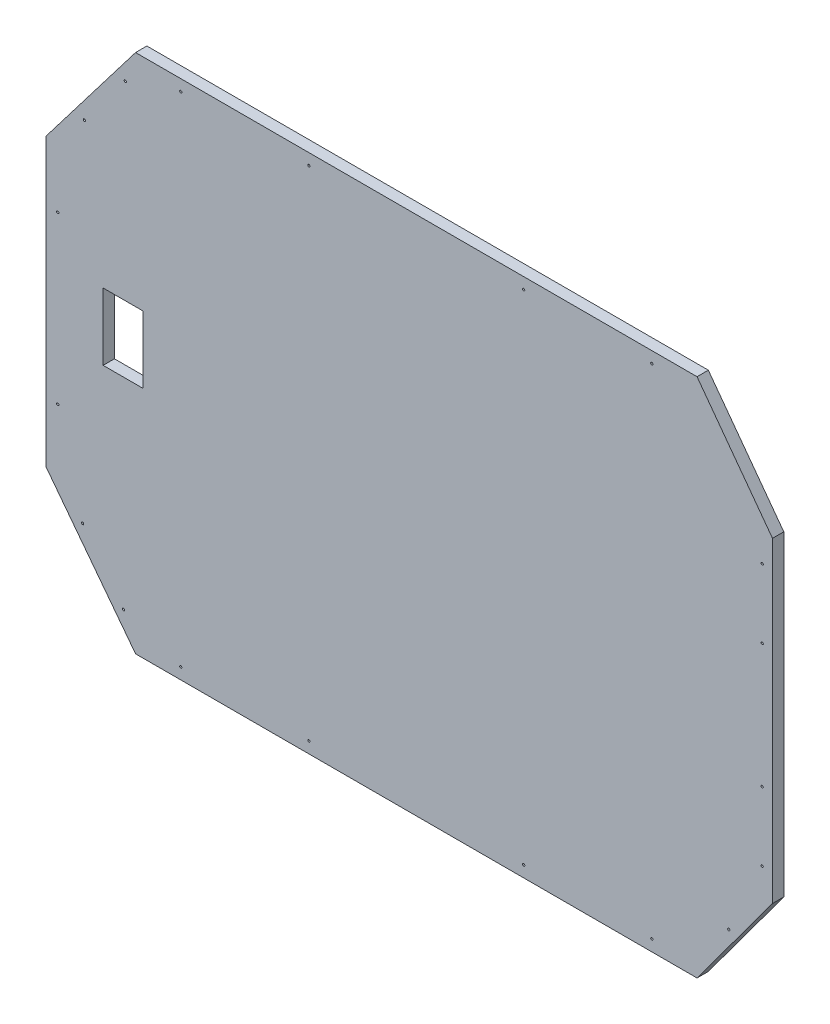
SolidWorks part; units mm, degrees
ref_plane "Front Plane" through (0, 0, 0) normal (0, 0, 1) x (1, 0, 0)
ref_plane "Top Plane" through (0, 0, 0) normal (0, 1, 0) x (1, 0, 0)
ref_plane "Right Plane" through (0, 0, 0) normal (1, 0, 0) x (0, 0, -1)
sketch "Sketch1" plane through (0, 0, 0) normal (0, 0, 1) x (1, 0, 0)
  line L0 (118.58, 345.4877) -> (863.58, 345.4877) construction
  line L1 (0, 500.6804) -> (118.58, 345.4877) construction
  line L2 (0, 881.2704) -> (0, 500.6804) construction
  line L3 (118.58, 1036.4632) -> (0, 881.2704) construction
  line L4 (863.58, 1036.4632) -> (118.58, 1036.4632) construction
  line L5 (963.71, 900.8043) -> (863.58, 1036.4632) construction
  line L6 (963.71, 481.1465) -> (963.71, 900.8043) construction
  line L7 (863.58, 345.4877) -> (963.71, 481.1465) construction
  line L8 (118.58, 345.4877) -> (863.58, 345.4877)
  line L9 (0, 500.6804) -> (118.58, 345.4877)
  line L10 (0, 881.2704) -> (0, 500.6804)
  line L11 (118.58, 1036.4632) -> (0, 881.2704)
  line L12 (863.58, 1036.4632) -> (118.58, 1036.4632)
  line L13 (963.71, 900.8043) -> (863.58, 1036.4632)
  line L14 (963.71, 481.1465) -> (963.71, 900.8043)
  line L15 (863.58, 345.4877) -> (963.71, 481.1465)
  line L60 (52.1694, 933.0769) -> (44.2234, 939.1483)
  line L61 (44.2234, 939.1483) -> (2.5279, 884.5789)
  line L62 (2.5279, 884.5789) -> (2.5279, 710.9754)
  line L63 (2.5279, 710.9754) -> (32.5279, 710.9754)
  line L64 (32.5279, 710.9754) -> (32.5279, 680.9754)
  line L65 (32.5279, 680.9754) -> (2.5279, 680.9754)
  line L66 (2.5279, 680.9754) -> (2.5279, 507.372)
  line L67 (2.5279, 507.372) -> (44.2234, 452.8026)
  line L68 (44.2234, 452.8026) -> (52.1694, 458.874)
  line L69 (52.1694, 458.874) -> (52.236, 458.7868)
  line L70 (52.236, 458.7868) -> (91.9659, 489.1436)
  line L71 (91.9659, 489.1436) -> (128.8173, 440.9139)
  line L72 (128.8173, 440.9139) -> (81.1415, 404.4857)
  line L73 (81.1415, 404.4857) -> (118.58, 355.4877)
  line L74 (118.58, 355.4877) -> (247.5279, 355.4877)
  line L75 (247.5279, 355.4877) -> (247.5279, 421.1462)
  line L76 (247.5279, 421.1462) -> (301.5406, 421.1462)
  line L77 (301.5406, 421.1462) -> (301.5406, 355.4877)
  line L78 (301.5406, 355.4877) -> (439.5279, 355.4877)
  line L79 (439.5279, 355.4877) -> (439.5279, 385.4877)
  line L80 (439.5279, 385.4877) -> (469.5279, 385.4877)
  line L81 (469.5279, 385.4877) -> (469.5279, 355.4877)
  line L82 (469.5279, 355.4877) -> (501.5406, 355.4877)
  line L83 (501.5406, 355.4877) -> (501.5406, 421.1462)
  line L84 (501.5406, 421.1462) -> (555.5406, 421.1462)
  line L85 (555.5406, 421.1462) -> (555.5406, 355.4877)
  line L86 (555.5406, 355.4877) -> (858.5839, 355.4877)
  line L87 (858.5839, 355.4877) -> (894.7004, 404.4193)
  line L88 (894.7004, 404.4193) -> (852.6416, 435.4629)
  line L89 (852.6416, 435.4629) -> (885.5391, 480.0333)
  line L90 (885.5391, 480.0333) -> (927.5979, 448.9897)
  line L91 (927.5979, 448.9897) -> (956.2379, 487.792)
  line L92 (956.2379, 487.792) -> (956.2379, 680.9754)
  line L93 (956.2379, 680.9754) -> (926.2379, 680.9754)
  line L94 (926.2379, 680.9754) -> (926.2379, 710.9754)
  line L95 (926.2379, 710.9754) -> (956.2379, 710.9754)
  line L96 (956.2379, 710.9754) -> (956.2379, 904.1589)
  line L97 (956.2379, 904.1589) -> (927.5979, 942.9612)
  line L98 (927.5979, 942.9612) -> (885.5391, 911.9176)
  line L99 (885.5391, 911.9176) -> (852.6416, 956.4879)
  line L100 (852.6416, 956.4879) -> (894.7004, 987.5316)
  line L101 (894.7004, 987.5316) -> (858.5839, 1036.4632)
  line L102 (858.5839, 1036.4632) -> (555.5406, 1036.4632)
  line L103 (555.5406, 1036.4632) -> (555.5406, 970.8046)
  line L104 (555.5406, 970.8046) -> (501.5406, 970.8046)
  line L105 (501.5406, 970.8046) -> (501.5406, 1036.4632)
  line L106 (501.5406, 1036.4632) -> (469.5279, 1036.4632)
  line L107 (469.5279, 1036.4632) -> (469.5279, 1006.4632)
  line L108 (469.5279, 1006.4632) -> (439.5279, 1006.4632)
  line L109 (439.5279, 1006.4632) -> (439.5279, 1036.4632)
  line L110 (439.5279, 1036.4632) -> (301.5406, 1036.4632)
  line L111 (301.5406, 1036.4632) -> (301.5406, 970.8046)
  line L112 (301.5406, 970.8046) -> (247.5279, 970.8046)
  line L113 (247.5279, 970.8046) -> (247.5279, 1036.4632)
  line L114 (247.5279, 1036.4632) -> (118.58, 1036.4632)
  line L115 (118.58, 1036.4632) -> (81.1415, 987.4652)
  line L116 (81.1415, 987.4652) -> (128.8173, 951.0369)
  line L117 (128.8173, 951.0369) -> (91.9659, 902.8072)
  line L118 (91.9659, 902.8072) -> (52.236, 933.1641)
  line L119 (52.236, 933.1641) -> (52.1694, 933.0769)
  line L120 (52.1694, 933.0769) -> (44.2234, 939.1483)
  line L121 (44.2234, 939.1483) -> (2.5279, 884.5789)
  line L122 (2.5279, 884.5789) -> (2.5279, 710.9754)
  line L123 (2.5279, 710.9754) -> (32.5279, 710.9754)
  line L124 (32.5279, 710.9754) -> (32.5279, 680.9754)
  line L125 (32.5279, 680.9754) -> (2.5279, 680.9754)
  line L126 (2.5279, 680.9754) -> (2.5279, 507.372)
  line L127 (2.5279, 507.372) -> (44.2234, 452.8026)
  line L128 (44.2234, 452.8026) -> (52.1694, 458.874)
  line L129 (52.1694, 458.874) -> (52.236, 458.7868)
  line L130 (52.236, 458.7868) -> (91.9659, 489.1436)
  line L131 (91.9659, 489.1436) -> (128.8173, 440.9139)
  line L132 (128.8173, 440.9139) -> (81.1415, 404.4857)
  line L133 (81.1415, 404.4857) -> (118.58, 355.4877)
  line L134 (118.58, 355.4877) -> (247.5279, 355.4877)
  line L135 (247.5279, 355.4877) -> (247.5279, 421.1462)
  line L136 (247.5279, 421.1462) -> (301.5406, 421.1462)
  line L137 (301.5406, 421.1462) -> (301.5406, 355.4877)
  line L138 (301.5406, 355.4877) -> (439.5279, 355.4877)
  line L139 (439.5279, 355.4877) -> (439.5279, 385.4877)
  line L140 (439.5279, 385.4877) -> (469.5279, 385.4877)
  line L141 (469.5279, 385.4877) -> (469.5279, 355.4877)
  line L142 (469.5279, 355.4877) -> (501.5406, 355.4877)
  line L143 (501.5406, 355.4877) -> (501.5406, 421.1462)
  line L144 (501.5406, 421.1462) -> (555.5406, 421.1462)
  line L145 (555.5406, 421.1462) -> (555.5406, 355.4877)
  line L146 (555.5406, 355.4877) -> (858.5839, 355.4877)
  line L147 (858.5839, 355.4877) -> (894.7004, 404.4193)
  line L148 (894.7004, 404.4193) -> (852.6416, 435.4629)
  line L149 (852.6416, 435.4629) -> (885.5391, 480.0333)
  line L150 (885.5391, 480.0333) -> (927.5979, 448.9897)
  line L151 (927.5979, 448.9897) -> (956.2379, 487.792)
  line L152 (956.2379, 487.792) -> (956.2379, 680.9754)
  line L153 (956.2379, 680.9754) -> (926.2379, 680.9754)
  line L154 (926.2379, 680.9754) -> (926.2379, 710.9754)
  line L155 (926.2379, 710.9754) -> (956.2379, 710.9754)
  line L156 (956.2379, 710.9754) -> (956.2379, 904.1589)
  line L157 (956.2379, 904.1589) -> (927.5979, 942.9612)
  line L158 (927.5979, 942.9612) -> (885.5391, 911.9176)
  line L159 (885.5391, 911.9176) -> (852.6416, 956.4879)
  line L160 (852.6416, 956.4879) -> (894.7004, 987.5316)
  line L161 (894.7004, 987.5316) -> (858.5839, 1036.4632)
  line L162 (858.5839, 1036.4632) -> (555.5406, 1036.4632)
  line L163 (555.5406, 1036.4632) -> (555.5406, 970.8046)
  line L164 (555.5406, 970.8046) -> (501.5406, 970.8046)
  line L165 (501.5406, 970.8046) -> (501.5406, 1036.4632)
  line L166 (501.5406, 1036.4632) -> (469.5279, 1036.4632)
  line L167 (469.5279, 1036.4632) -> (469.5279, 1006.4632)
  line L168 (469.5279, 1006.4632) -> (439.5279, 1006.4632)
  line L169 (439.5279, 1006.4632) -> (439.5279, 1036.4632)
  line L170 (439.5279, 1036.4632) -> (301.5406, 1036.4632)
  line L171 (301.5406, 1036.4632) -> (301.5406, 970.8046)
  line L172 (301.5406, 970.8046) -> (247.5279, 970.8046)
  line L173 (247.5279, 970.8046) -> (247.5279, 1036.4632)
  line L174 (247.5279, 1036.4632) -> (118.58, 1036.4632)
  line L175 (118.58, 1036.4632) -> (81.1415, 987.4652)
  line L176 (81.1415, 987.4652) -> (128.8173, 951.0369)
  line L177 (128.8173, 951.0369) -> (91.9659, 902.8072)
  line L178 (91.9659, 902.8072) -> (52.236, 933.1641)
  line L179 (52.236, 933.1641) -> (52.1694, 933.0769)
  circle A0 centre (633.58, 360.4877) radius 1.5 construction
  circle A1 centre (348.58, 360.4877) radius 1.5 construction
  circle A2 centre (178.58, 360.4877) radius 1.5 construction
  arc A3 (101.5789, 389.644) -> (103.3851, 387.2486) centre (102.482, 388.4463) ccw construction
  arc A4 (103.3851, 387.2486) -> (101.5789, 389.644) centre (102.482, 388.4463) ccw construction
  arc A5 (49.1995, 459.109) -> (47.3933, 461.5044) centre (48.2964, 460.3067) ccw construction
  arc A6 (47.3933, 461.5044) -> (49.1995, 459.109) centre (48.2964, 460.3067) ccw construction
  arc A7 (15.3287, 579.1804) -> (15.3287, 582.1804) centre (15.3287, 580.6804) ccw construction
  arc A8 (15.3287, 582.1804) -> (15.3287, 579.1804) centre (15.3287, 580.6804) ccw construction
  arc A9 (15.3287, 799.7704) -> (15.3287, 802.7704) centre (15.3287, 801.2704) ccw construction
  arc A10 (15.3287, 802.7704) -> (15.3287, 799.7704) centre (15.3287, 801.2704) ccw construction
  arc A11 (51.6031, 926.0294) -> (49.7969, 923.6341) centre (50.7, 924.8318) ccw construction
  arc A12 (49.7969, 923.6341) -> (51.6031, 926.0294) centre (50.7, 924.8318) ccw construction
  arc A13 (105.7887, 997.8898) -> (103.9825, 995.4945) centre (104.8856, 996.6922) ccw construction
  arc A14 (103.9825, 995.4945) -> (105.7887, 997.8898) centre (104.8856, 996.6922) ccw construction
  circle A15 centre (178.58, 1021.4632) radius 1.5 construction
  circle A16 centre (348.58, 1021.4632) radius 1.5 construction
  circle A17 centre (633.58, 1021.4632) radius 1.5 construction
  circle A18 centre (803.58, 1021.4632) radius 1.5 construction
  circle A19 centre (905.6543, 959.6921) radius 1.5 construction
  circle A20 centre (950.0195, 864.7409) radius 1.5 construction
  circle A21 centre (950.0195, 773.3269) radius 1.5 construction
  circle A22 centre (950.0195, 608.6349) radius 1.5 construction
  circle A23 centre (950.0195, 517.2209) radius 1.5 construction
  circle A24 centre (803.58, 360.4877) radius 1.5 construction
  circle A25 centre (905.6543, 422.2697) radius 1.5 construction
  circle A26 centre (633.58, 360.4877) radius 1.5
  circle A27 centre (348.58, 360.4877) radius 1.5
  circle A28 centre (178.58, 360.4877) radius 1.5
  arc A29 (101.5789, 389.644) -> (103.3851, 387.2486) centre (102.482, 388.4463) ccw
  arc A30 (103.3851, 387.2486) -> (101.5789, 389.644) centre (102.482, 388.4463) ccw
  arc A31 (49.1995, 459.109) -> (47.3933, 461.5044) centre (48.2964, 460.3067) ccw
  arc A32 (47.3933, 461.5044) -> (49.1995, 459.109) centre (48.2964, 460.3067) ccw
  arc A33 (15.3287, 579.1804) -> (15.3287, 582.1804) centre (15.3287, 580.6804) ccw
  arc A34 (15.3287, 582.1804) -> (15.3287, 579.1804) centre (15.3287, 580.6804) ccw
  arc A35 (15.3287, 799.7704) -> (15.3287, 802.7704) centre (15.3287, 801.2704) ccw
  arc A36 (15.3287, 802.7704) -> (15.3287, 799.7704) centre (15.3287, 801.2704) ccw
  arc A37 (51.6031, 926.0294) -> (49.7969, 923.6341) centre (50.7, 924.8318) ccw
  arc A38 (49.7969, 923.6341) -> (51.6031, 926.0294) centre (50.7, 924.8318) ccw
  arc A39 (105.7887, 997.8898) -> (103.9825, 995.4945) centre (104.8856, 996.6922) ccw
  arc A40 (103.9825, 995.4945) -> (105.7887, 997.8898) centre (104.8856, 996.6922) ccw
  circle A41 centre (178.58, 1021.4632) radius 1.5
  circle A42 centre (348.58, 1021.4632) radius 1.5
  circle A43 centre (633.58, 1021.4632) radius 1.5
  circle A44 centre (803.58, 1021.4632) radius 1.5
  circle A45 centre (905.6543, 959.6921) radius 1.5
  circle A46 centre (950.0195, 864.7409) radius 1.5
  circle A47 centre (950.0195, 773.3269) radius 1.5
  circle A48 centre (950.0195, 608.6349) radius 1.5
  circle A49 centre (950.0195, 517.2209) radius 1.5
  circle A50 centre (803.58, 360.4877) radius 1.5
  circle A51 centre (905.6543, 422.2697) radius 1.5
  dimension "D1" = 0
sketch "Sketch2" plane through (0, 0, 0) normal (0, 0, 1) x (1, 0, 0)
  line L0 (0, 500.6804) -> (118.58, 345.4877) construction
  line L1 (118.58, 345.4877) -> (863.58, 345.4877) construction
  line L2 (863.58, 345.4877) -> (963.71, 481.1465) construction
  line L3 (963.71, 481.1465) -> (963.71, 900.8043) construction
  line L4 (963.71, 900.8043) -> (863.58, 1036.4632) construction
  line L5 (863.58, 1036.4632) -> (118.58, 1036.4632) construction
  line L6 (118.58, 1036.4632) -> (0, 881.2704) construction
  line L7 (0, 881.2704) -> (0, 500.6804) construction
  line L8 (0, 500.6804) -> (118.58, 345.4877)
  line L9 (118.58, 345.4877) -> (863.58, 345.4877)
  line L10 (863.58, 345.4877) -> (963.71, 481.1465)
  line L11 (963.71, 481.1465) -> (963.71, 900.8043)
  line L12 (963.71, 900.8043) -> (863.58, 1036.4632)
  line L13 (863.58, 1036.4632) -> (118.58, 1036.4632)
  line L14 (118.58, 1036.4632) -> (0, 881.2704)
  line L15 (0, 881.2704) -> (0, 500.6804)
extrude "Boss-Extrude1" add sketch "Sketch2" along normal blind 15
sketch "Sketch7" plane through (0, 0, 0) normal (0, 0, -1) x (-1, 0, 0)
  line L8 (0, 500.6804) -> (0, 881.2704)
  line L9 (0, 881.2704) -> (-118.58, 1036.4632)
  line L10 (-118.58, 1036.4632) -> (-863.58, 1036.4632)
  line L11 (-863.58, 1036.4632) -> (-963.71, 900.8043)
  line L12 (-963.71, 900.8043) -> (-963.71, 481.1465)
  line L13 (-963.71, 481.1465) -> (-863.58, 345.4877)
  line L14 (-863.58, 345.4877) -> (-118.58, 345.4877)
  line L15 (-118.58, 345.4877) -> (0, 500.6804)
  line L16 (0, 500.6804) -> (0, 881.2704)
  line L17 (0, 881.2704) -> (-118.58, 1036.4632)
  line L18 (-118.58, 1036.4632) -> (-863.58, 1036.4632)
  line L19 (-863.58, 1036.4632) -> (-963.71, 900.8043)
  line L20 (-963.71, 900.8043) -> (-963.71, 481.1465)
  line L21 (-963.71, 481.1465) -> (-863.58, 345.4877)
  line L22 (-863.58, 345.4877) -> (-118.58, 345.4877)
  line L23 (-118.58, 345.4877) -> (0, 500.6804)
  circle A0 centre (-950.0195, 773.3269) radius 1.5 construction
  circle A1 centre (-950.0195, 773.3269) radius 1.5
  arc A2 (-15.3287, 579.1804) -> (-15.3287, 582.1804) centre (-15.3287, 580.6804) ccw construction
  arc A3 (-15.3287, 582.1804) -> (-15.3287, 579.1804) centre (-15.3287, 580.6804) ccw construction
  arc A4 (-47.3933, 461.5044) -> (-49.1995, 459.109) centre (-48.2964, 460.3067) ccw construction
  arc A5 (-101.5789, 389.644) -> (-103.3851, 387.2486) centre (-102.482, 388.4463) ccw construction
  arc A6 (-103.3851, 387.2486) -> (-101.5789, 389.644) centre (-102.482, 388.4463) ccw construction
  circle A7 centre (-178.58, 360.4877) radius 1.5 construction
  circle A8 centre (-348.58, 360.4877) radius 1.5 construction
  circle A9 centre (-633.58, 360.4877) radius 1.5 construction
  circle A10 centre (-803.58, 360.4877) radius 1.5 construction
  circle A11 centre (-905.6543, 422.2697) radius 1.5 construction
  circle A12 centre (-950.0195, 517.2209) radius 1.5 construction
  circle A13 centre (-950.0195, 608.6349) radius 1.5 construction
  circle A14 centre (-950.0195, 864.7409) radius 1.5 construction
  arc A15 (-15.3287, 579.1804) -> (-15.3287, 582.1804) centre (-15.3287, 580.6804) ccw
  arc A16 (-15.3287, 582.1804) -> (-15.3287, 579.1804) centre (-15.3287, 580.6804) ccw
  arc A17 (-47.3933, 461.5044) -> (-49.1995, 459.109) centre (-48.2964, 460.3067) ccw
  arc A18 (-101.5789, 389.644) -> (-103.3851, 387.2486) centre (-102.482, 388.4463) ccw
  arc A19 (-103.3851, 387.2486) -> (-101.5789, 389.644) centre (-102.482, 388.4463) ccw
  circle A20 centre (-178.58, 360.4877) radius 1.5
  circle A21 centre (-348.58, 360.4877) radius 1.5
  circle A22 centre (-633.58, 360.4877) radius 1.5
  circle A23 centre (-803.58, 360.4877) radius 1.5
  circle A24 centre (-905.6543, 422.2697) radius 1.5
  circle A25 centre (-950.0195, 517.2209) radius 1.5
  circle A26 centre (-950.0195, 608.6349) radius 1.5
  circle A27 centre (-950.0195, 864.7409) radius 1.5
  point P8 (-47.3933, 461.5044)
  point P10 (-48.2964, 460.3067)
  point P12 (-102.482, 388.4463)
  point P14 (-103.3851, 387.2486)
  point P15 (-950.0195, 864.7409)
  dimension "D1" = 0
sketch "Sketch9" plane through (0, 0, 0) normal (0, 0, -1) x (-1, 0, 0)
  circle A0 centre (-803.58, 1021.4632) radius 1.5 construction
  circle A1 centre (-633.58, 1021.4632) radius 1.5 construction
  circle A2 centre (-348.58, 1021.4632) radius 1.5 construction
  circle A3 centre (-178.58, 1021.4632) radius 1.5 construction
  arc A4 (-49.7969, 923.6341) -> (-51.6031, 926.0294) centre (-50.7, 924.8318) ccw construction
  arc A5 (-51.6031, 926.0294) -> (-49.7969, 923.6341) centre (-50.7, 924.8318) ccw construction
  arc A6 (-103.9825, 995.4945) -> (-105.7887, 997.8898) centre (-104.8856, 996.6922) ccw construction
  arc A7 (-105.7887, 997.8898) -> (-103.9825, 995.4945) centre (-104.8856, 996.6922) ccw construction
  arc A8 (-15.3287, 802.7704) -> (-15.3287, 799.7704) centre (-15.3287, 801.2704) ccw construction
  arc A9 (-15.3287, 799.7704) -> (-15.3287, 802.7704) centre (-15.3287, 801.2704) ccw construction
  arc A10 (-15.3287, 582.1804) -> (-15.3287, 579.1804) centre (-15.3287, 580.6804) ccw construction
  arc A11 (-15.3287, 579.1804) -> (-15.3287, 582.1804) centre (-15.3287, 580.6804) ccw construction
  arc A12 (-49.1995, 459.109) -> (-47.3933, 461.5044) centre (-48.2964, 460.3067) ccw construction
  arc A13 (-47.3933, 461.5044) -> (-49.1995, 459.109) centre (-48.2964, 460.3067) ccw construction
  arc A14 (-103.3851, 387.2486) -> (-101.5789, 389.644) centre (-102.482, 388.4463) ccw construction
  arc A15 (-101.5789, 389.644) -> (-103.3851, 387.2486) centre (-102.482, 388.4463) ccw construction
  circle A16 centre (-178.58, 360.4877) radius 1.5 construction
  circle A17 centre (-348.58, 360.4877) radius 1.5 construction
  circle A18 centre (-633.58, 360.4877) radius 1.5 construction
  circle A19 centre (-803.58, 360.4877) radius 1.5 construction
  circle A20 centre (-905.6543, 422.2697) radius 1.5 construction
  circle A21 centre (-950.0195, 517.2209) radius 1.5 construction
  circle A22 centre (-950.0195, 864.7409) radius 1.5 construction
  circle A23 centre (-950.0195, 773.3269) radius 1.5 construction
  circle A24 centre (-950.0195, 608.6349) radius 1.5 construction
  circle A25 centre (-803.58, 1021.4632) radius 1.5
  circle A26 centre (-633.58, 1021.4632) radius 1.5
  circle A27 centre (-348.58, 1021.4632) radius 1.5
  circle A28 centre (-178.58, 1021.4632) radius 1.5
  arc A29 (-49.7969, 923.6341) -> (-51.6031, 926.0294) centre (-50.7, 924.8318) ccw
  arc A30 (-51.6031, 926.0294) -> (-49.7969, 923.6341) centre (-50.7, 924.8318) ccw
  arc A31 (-103.9825, 995.4945) -> (-105.7887, 997.8898) centre (-104.8856, 996.6922) ccw
  arc A32 (-105.7887, 997.8898) -> (-103.9825, 995.4945) centre (-104.8856, 996.6922) ccw
  arc A33 (-15.3287, 802.7704) -> (-15.3287, 799.7704) centre (-15.3287, 801.2704) ccw
  arc A34 (-15.3287, 799.7704) -> (-15.3287, 802.7704) centre (-15.3287, 801.2704) ccw
  arc A35 (-15.3287, 582.1804) -> (-15.3287, 579.1804) centre (-15.3287, 580.6804) ccw
  arc A36 (-15.3287, 579.1804) -> (-15.3287, 582.1804) centre (-15.3287, 580.6804) ccw
  arc A37 (-49.1995, 459.109) -> (-47.3933, 461.5044) centre (-48.2964, 460.3067) ccw
  arc A38 (-47.3933, 461.5044) -> (-49.1995, 459.109) centre (-48.2964, 460.3067) ccw
  arc A39 (-103.3851, 387.2486) -> (-101.5789, 389.644) centre (-102.482, 388.4463) ccw
  arc A40 (-101.5789, 389.644) -> (-103.3851, 387.2486) centre (-102.482, 388.4463) ccw
  circle A41 centre (-178.58, 360.4877) radius 1.5
  circle A42 centre (-348.58, 360.4877) radius 1.5
  circle A43 centre (-633.58, 360.4877) radius 1.5
  circle A44 centre (-803.58, 360.4877) radius 1.5
  circle A45 centre (-905.6543, 422.2697) radius 1.5
  circle A46 centre (-950.0195, 517.2209) radius 1.5
  circle A47 centre (-950.0195, 864.7409) radius 1.5
  circle A48 centre (-950.0195, 773.3269) radius 1.5
  circle A49 centre (-950.0195, 608.6349) radius 1.5
  point P2 (-950.0195, 517.2209)
extrude "Cut-Extrude1" cut sketch "Sketch9" against normal through all and the other way through all
sketch "Sketch10" plane through (0, 0, 0) normal (0, 0, -1) x (-1, 0, 0)
  line L0 (0, 881.2704) -> (0, 500.6804) construction
  line L1 (-128.15, 744.3942) -> (-75.55, 744.3942)
  line L2 (-128.15, 744.3942) -> (-128.15, 655.4942)
  line L3 (-128.15, 655.4942) -> (-75.55, 655.4942)
  line L4 (-75.55, 744.3942) -> (-75.55, 655.4942)
  line L5 (-118.58, 345.4877) -> (-863.58, 345.4877) construction
  dimension "D1" = 52.6
  dimension "D2" = 88.9
  dimension "D3" = 75.55
  dimension "D4" = 310.0065
extrude "Cut-Extrude2" cut sketch "Sketch10" against normal through all
